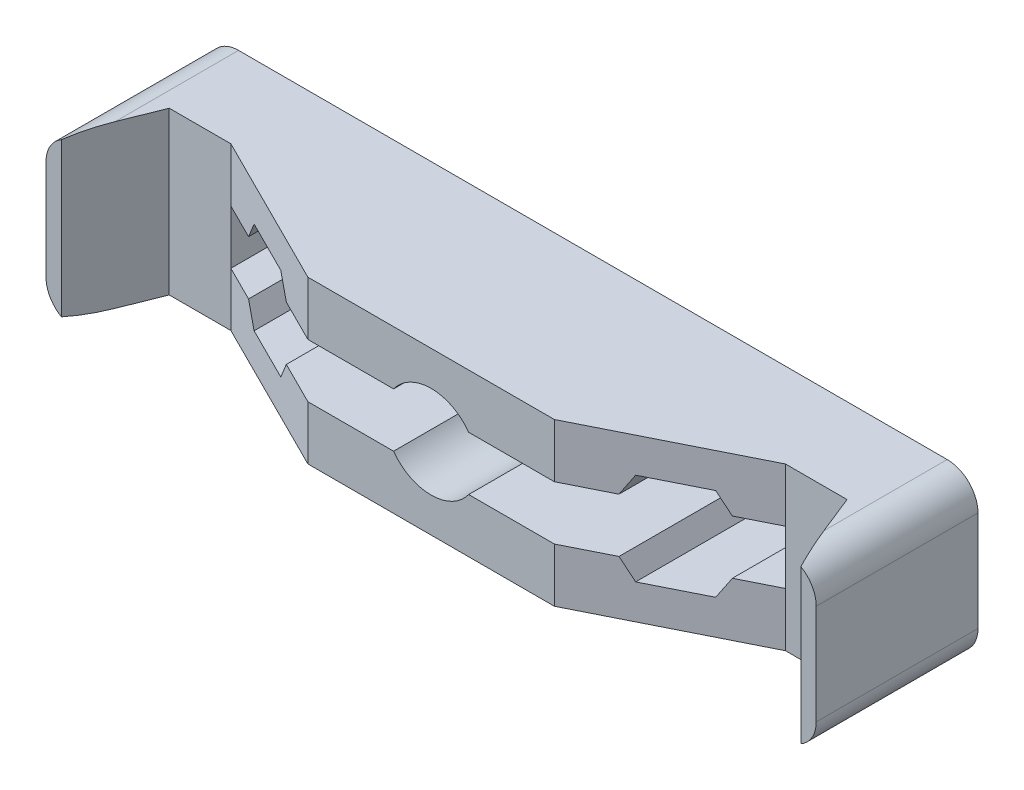
SolidWorks part; units mm, degrees
ref_plane "正面" through (0, 0, 0) normal (0, 0, 1) x (1, 0, 0)
ref_plane "平面" through (0, 0, 0) normal (0, 1, 0) x (1, 0, 0)
ref_plane "右側面" through (0, 0, 0) normal (1, 0, 0) x (0, 0, -1)
sketch "ｽｹｯﾁ1" plane through (0, 0, 0) normal (0, 0, 1) x (1, 0, 0)
  line L5 (0, 0) -> (50, 0)
  line L6 (0, 0) -> (0, 10.5)
  line L7 (0, 10.5) -> (50, 10.5)
  line L8 (50, 0) -> (50, 10.5)
  dimension "D1" = 10.5
  dimension "D2" = 50
extrude "ﾎﾞｽ - 押し出し1" add sketch "ｽｹｯﾁ1" along normal blind 17
sketch "ｽｹｯﾁ2" plane through (0, 0, 17) normal (0, 0, 1) x (1, 0, 0)
  line L0 (0, 5.25) -> (50, 5.25) construction
  line L1 (0, 10.5) -> (0, 0) construction
  line L2 (50, 0) -> (50, 10.5) construction
  line L3 (25, 10.5) -> (25, 0) construction
  line L4 (50, 10.5) -> (0, 10.5) construction
  line L5 (0, 0) -> (50, 0) construction
  line L11 (7, 3.5) -> (43, 3.5)
  line L12 (7, 3.5) -> (7, 7)
  line L13 (7, 7) -> (43, 7)
  line L14 (43, 3.5) -> (43, 7)
  line L15 (7, 3.5) -> (43, 7) construction
  line L16 (7, 7) -> (43, 3.5) construction
  point P12 (25, 5.25)
  point P17 (25, 5.25)
  dimension "D1" = 3.5
  dimension "D2" = 36
extrude "ｶｯﾄ - 押し出し1" cut sketch "ｽｹｯﾁ2" against normal blind 10
sketch "ｽｹｯﾁ3" plane through (0, 0, 0) normal (0, -1, 0) x (1, 0, 0)
  line L0 (1, 17) -> (3, 12)
  line L1 (0, 17) -> (50, 17) construction
  line L2 (3, 12) -> (7, 12)
  line L3 (7, 12) -> (17, 17)
  line L4 (17, 17) -> (1, 17)
  line L5 (33, 17) -> (43, 12)
  line L6 (43, 12) -> (47, 12)
  line L7 (47, 12) -> (49, 17)
  line L8 (49, 17) -> (33, 17)
  line L9 (0, 17) -> (0, 0) construction
  line L10 (50, 17) -> (50, 0) construction
  dimension "D1" = 1
  dimension "D2" = 1
  dimension "D3" = 3
  dimension "D4" = 3
  dimension "D5" = 17
  dimension "D6" = 17
  dimension "D7" = 5
  dimension "D8" = 5
  dimension "D9" = 7
  dimension "D10" = 7
extrude "ｶｯﾄ - 押し出し2" cut sketch "ｽｹｯﾁ3" against normal up to surface (10.5 mm away) up to face at (25, 10.5, 8.5)
sketch "ｽｹｯﾁ4" plane through (0, 0, 0) normal (0, 0, -1) x (-1, 0, 0)
  line L0 (-25, 0) -> (-25, 10.5) construction
  line L1 (0, 0) -> (-50, 0) construction
  line L2 (-50, 10.5) -> (0, 10.5) construction
  line L3 (0, 5.25) -> (-50, 5.25) construction
  line L4 (0, 10.5) -> (0, 0) construction
  line L5 (-50, 0) -> (-50, 10.5) construction
  line L6 (-0.4, 5.25) -> (-3.9, 5.25) construction
  line L7 (-0.4, 8.5) -> (-3.9, 8.5)
  line L8 (-0.4, 8.5) -> (-0.4, 2)
  line L9 (-0.4, 2) -> (-3.9, 2)
  line L10 (-3.9, 8.5) -> (-3.9, 2)
  line L11 (-2.15, 2) -> (-2.15, 8.5) construction
  line L12 (-49.6, 8.5) -> (-49.6, 2)
  line L13 (-49.6, 2) -> (-46.1, 2)
  line L14 (-46.1, 8.5) -> (-46.1, 2)
  line L15 (-49.6, 8.5) -> (-46.1, 8.5)
  dimension "D1" = 3.5
  dimension "D2" = 6.5
  dimension "D3" = 0.4
extrude "ｶｯﾄ - 押し出し3" cut sketch "ｽｹｯﾁ4" against normal blind 6.5
fillet "ﾌｨﾚｯﾄ1" radius 2 4 edges at (0, 0, 8.5) (0, 10.5, 8.5) (50, 0, 8.5) (50, 10.5, 8.5)
ref_plane "この面でカットした部品を印刷" through (0, 0, 6.5) normal (0, 0, -1) x (-1, 0, 0)
sketch "ｽｹｯﾁ6" plane through (0, 0, 0) normal (0, 0, -1) x (-1, 0, 0)
  line L0 (-50, 5.25) -> (0, 5.25) construction
  line L1 (-50, 2) -> (-50, 8.5) construction
  line L2 (0, 8.5) -> (0, 2) construction
  line L3 (-25, 10.5) -> (-25, 0) construction
  line L4 (-48, 10.5) -> (-2, 10.5) construction
  line L5 (-2, 0) -> (-48, 0) construction
  circle A0 centre (-25, 5.25) radius 3
  circle A1 centre (-11.75, 5.25) radius 1.75
  circle A2 centre (-38.25, 5.25) radius 1.75
  dimension "D1" = 6
  dimension "D2" = 3.5
  dimension "D3" = 3.5
  dimension "D4" = 13.25
  dimension "D5" = 13.25
extrude "ｶｯﾄ - 押し出し4" cut sketch "ｽｹｯﾁ6" against normal through all
sketch "ｽｹｯﾁ7" plane through (0, 0, 7) normal (0, 0, 1) x (1, 0, 0)
  line L0 (38.25, 7) -> (27.4367, 7) construction
  line L1 (34.7859, 5.25) -> (36.5179, 2.25)
  line L2 (36.5179, 2.25) -> (39.9821, 2.25)
  line L3 (39.9821, 2.25) -> (41.7141, 5.25)
  line L4 (41.7141, 5.25) -> (39.9821, 8.25)
  line L5 (39.9821, 8.25) -> (36.5179, 8.25)
  line L6 (36.5179, 8.25) -> (34.7859, 5.25)
  line L7 (43, 5.25) -> (7, 5.25) construction
  line L9 (43, 3.5) -> (43, 7) construction
  line L10 (7, 7) -> (7, 3.5) construction
  line L11 (25, 5.25) -> (25, 0.6326) construction
  line L12 (25, 5.25) -> (25, 9.2813) construction
  line L13 (13.4821, 8.25) -> (15.2141, 5.25)
  line L14 (10.0179, 8.25) -> (13.4821, 8.25)
  line L15 (8.2859, 5.25) -> (10.0179, 8.25)
  line L16 (10.0179, 2.25) -> (8.2859, 5.25)
  line L17 (13.4821, 2.25) -> (10.0179, 2.25)
  line L18 (15.2141, 5.25) -> (13.4821, 2.25)
  circle A0 centre (38.25, 5.25) radius 3 construction
  circle A1 centre (11.75, 5.25) radius 3 construction
  dimension "D1" = 6
  dimension "D2" = 120
extrude "ｶｯﾄ - 押し出し5" cut sketch "ｽｹｯﾁ7" along normal through all
sketch "ｽｹｯﾁ8" plane through (0, 0, 7) normal (0, 0, 1) x (1, 0, 0)
  line L0 (43, 5.25) -> (7, 5.25) construction
  line L1 (36.5179, 2.25) -> (39.9821, 2.25)
  line L2 (39.9821, 2.25) -> (41.7141, 5.25)
  line L3 (41.7141, 5.25) -> (39.9821, 8.25)
  line L4 (39.9821, 8.25) -> (36.5179, 8.25)
  line L5 (36.5179, 8.25) -> (34.7859, 5.25)
  line L6 (34.7859, 5.25) -> (36.5179, 2.25)
  line L7 (43, 3.5) -> (43, 7) construction
  line L8 (7, 7) -> (7, 3.5) construction
  line L9 (25, 5.25) -> (25, 3.6623) construction
  line L10 (15.2141, 5.25) -> (13.4821, 2.25)
  line L11 (13.4821, 8.25) -> (15.2141, 5.25)
  line L12 (10.0179, 8.25) -> (13.4821, 8.25)
  line L13 (8.2859, 5.25) -> (10.0179, 8.25)
  line L14 (10.0179, 2.25) -> (8.2859, 5.25)
  line L15 (13.4821, 2.25) -> (10.0179, 2.25)
  circle A0 centre (38.25, 5.25) radius 3 construction
  circle A1 centre (11.75, 5.25) radius 3 construction
extrude "ｶｯﾄ - 押し出し6" cut sketch "ｽｹｯﾁ8" against normal blind 3
sketch "ｽｹｯﾁ9" plane through (0, 0, 6.5) normal (0, 0, -1) x (-1, 0, 0)
  line L5 (-54.1814, -6.3116) -> (4.2397, -6.3116)
  line L6 (-54.1814, -6.3116) -> (-54.1814, 17.9335)
  line L7 (-54.1814, 17.9335) -> (4.2397, 17.9335)
  line L8 (4.2397, -6.3116) -> (4.2397, 17.9335)
extrude "ｶｯﾄ - 押し出し7" cut sketch "ｽｹｯﾁ9" along normal through all
